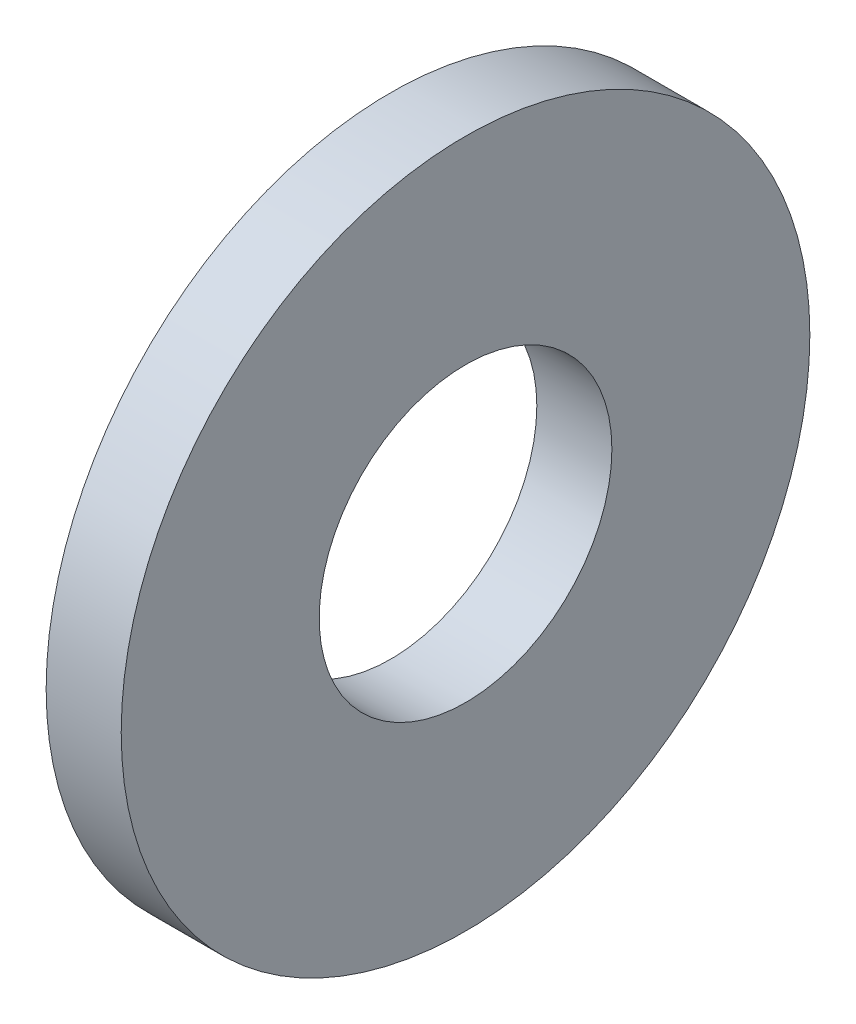
SolidWorks part; units mm, degrees
ref_plane "Front Plane" through (0, 0, 0) normal (0, 0, 1) x (1, 0, 0)
ref_plane "Top Plane" through (0, 0, 0) normal (0, 1, 0) x (1, 0, 0)
ref_plane "Right Plane" through (0, 0, 0) normal (1, 0, 0) x (0, 0, -1)
sketch "Sketch1" plane through (0, 0, 0) normal (1, 0, 0) x (0, 0, -1)
  circle A0 centre (0, 0) radius 9.3218
  circle A1 centre (0, 0) radius 3.9624
  dimension "OD" = 18.6436
  dimension "ID" = 7.9248
extrude "Boss-Extrude1" add sketch "Sketch1" along normal blind 2.032
